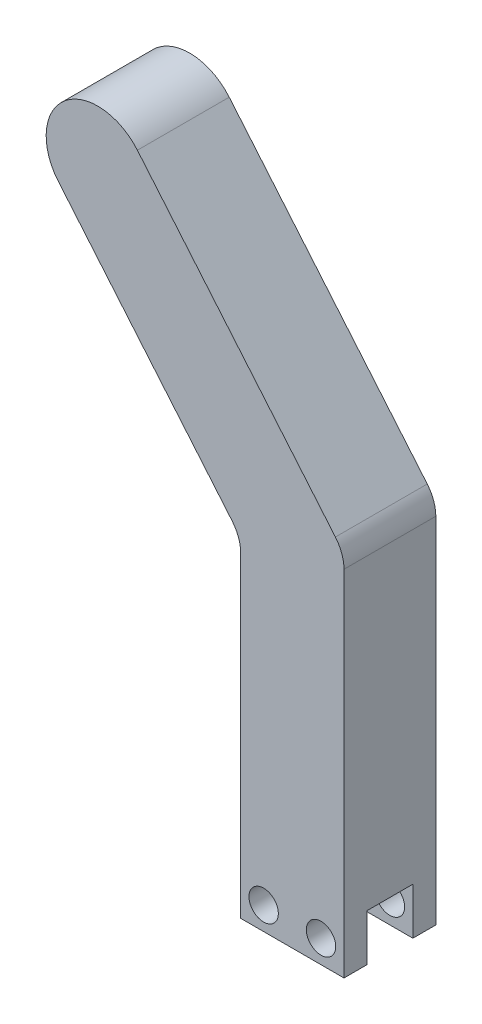
SolidWorks part; units mm, degrees
ref_plane "Front Plane" through (0, 0, 0) normal (0, 0, 1) x (1, 0, 0)
ref_plane "Top Plane" through (0, 0, 0) normal (0, 1, 0) x (1, 0, 0)
ref_plane "Right Plane" through (0, 0, 0) normal (1, 0, 0) x (0, 0, -1)
sketch "Sketch2" [suppressed] plane through (0, 0, 0) normal (0, 0, 1) x (1, 0, 0)
  line L0 (0, 0) -> (0, 12.7) construction
  line L3 (7.1437, 19.05) -> (7.1437, 0)
  line L7 (-7.1438, 0) -> (-7.1438, 19.05)
  line L11 (-7.1438, 19.05) -> (-24.6555, 33.7441)
  line L12 (-24.6555, 33.7441) -> (-49.6696, 38.1548)
  line L13 (7.1437, 19.05) -> (-20.6374, 42.3611)
  line L14 (-20.6374, 42.3611) -> (-48.0749, 47.1991)
  line L15 (-42.439, 46.2053) -> (-44.0337, 37.161) construction
  line L16 (-13.6197, 36.4726) -> (-19.523, 29.4374) construction
  circle A0 centre (0, 0) radius 3.9688
  arc A1 (7.1437, 0) -> (-7.1438, 0) centre (0, 0) cw
  circle A2 centre (0, 12.7) radius 3.175
  circle A4 centre (0, 0) radius 7.1438 construction
  arc A11 (-48.0749, 47.1991) -> (-49.6696, 38.1548) centre (-48.8723, 42.6769) ccw
  dimension "D1" = 7.1437
  dimension "D2" = 14.2875
  dimension "D3" = 6.35
  dimension "D4" = 7.9375
  dimension "D5" = 12.7
  dimension "D6" = 180
  dimension "D7" = 22.86
  dimension "D8" = 130
  dimension "D9" = 25.4
  dimension "D10" = 150
  dimension "D11" = 6.35
  dimension "D15" = 6.35
sketch "Sketch4" plane through (0, 0, 0) normal (0, 0, 1) x (1, 0, 0)
  line L0 (0, -6.35) -> (-14.2875, -6.35)
  line L1 (0, 0) -> (0, -6.35)
  line L2 (-14.2875, -6.35) -> (-14.2875, 0)
  line L3 (-14.2875, 0) -> (0, 0) construction
  line L4 (-14.2875, -3.175) -> (0, -3.175) construction
  line L5 (-3.175, -3.175) -> (-11.1125, -3.175)
  line L6 (0, 0) -> (0, 44.45)
  line L7 (0, 44.45) -> (-28.5719, 78.5007)
  line L8 (0, 44.45) -> (-14.2875, 39.2498) construction
  line L9 (-14.2875, 0) -> (-14.2875, 39.2498)
  line L10 (-14.2875, 39.2498) -> (-39.5168, 69.3168)
  line L11 (-28.5719, 78.5007) -> (-39.5168, 69.3168) construction
  arc A3 (-28.5719, 78.5007) -> (-39.5168, 69.3168) centre (-34.0443, 73.9088) ccw
  circle A4 centre (-11.1125, -3.175) radius 2.032
  circle A5 centre (-3.175, -3.175) radius 2.032
  point P11 (-7.1437, -3.175)
  dimension "D2" = 14.2875
  dimension "D3" = 6.35
  dimension "D4" = 44.45
  dimension "D10" = 4.064
  dimension "D11" = 4.064
  dimension "D5" = 44.45
  dimension "D7" = 70
  dimension "D8" = 3.175
  dimension "D9" = 3.175
  dimension "D6" = 140
extrude "Boss-Extrude1" add sketch "Sketch4" along normal blind 12.7
sketch "Sketch5" plane through (-14.2875, 0, 0) normal (-1, 0, 0) x (0, 0, 1)
  line L0 (9.525, -6.35) -> (3.175, -6.35)
  line L1 (12.7, -6.35) -> (0, -6.35) construction
  line L2 (3.175, -6.35) -> (3.175, 0.1219)
  line L3 (3.175, 0.1219) -> (9.525, 0.1219)
  line L4 (9.525, 0.1219) -> (9.525, -6.35)
  point P5 (6.35, -6.35)
  point P6 (6.35, -6.35)
  dimension "D1" = 6.35
  dimension "D2" = 6.4719
extrude "Cut-Extrude1" cut sketch "Sketch5" against normal through all
fillet "Fillet1" radius 5.08 2 edges at (0, 44.45, 6.35) (-14.2875, 39.2498, 6.35)
